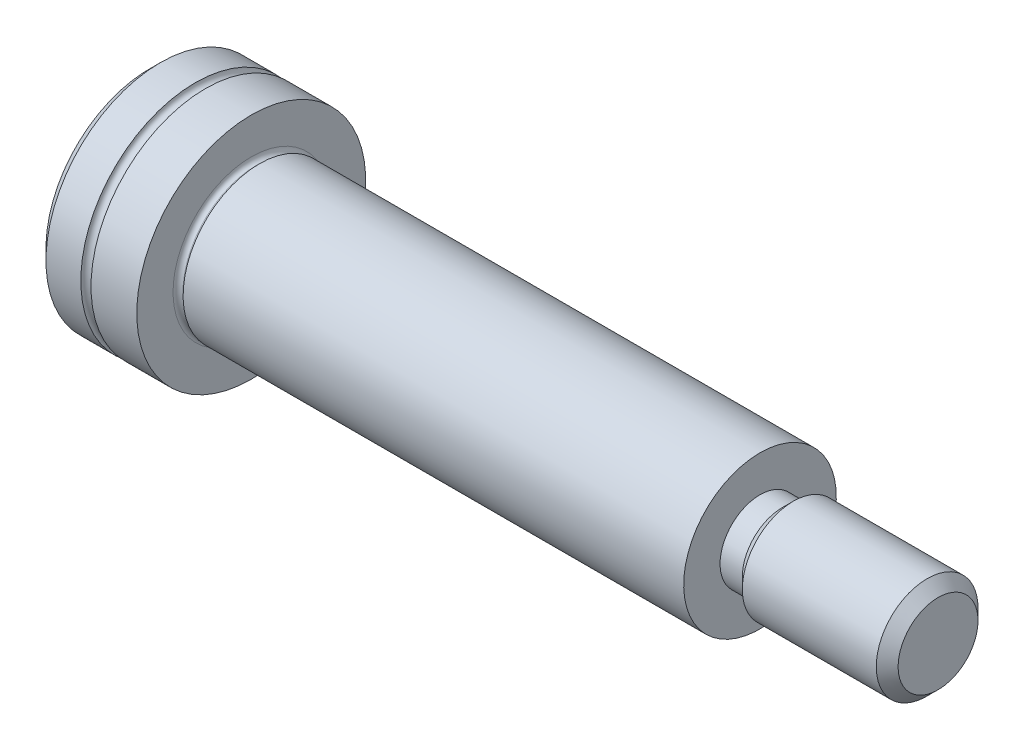
SolidWorks part; units mm, degrees
ref_plane "Front Plane" through (0, 0, 0) normal (0, 0, 1) x (1, 0, 0)
ref_plane "Top Plane" through (0, 0, 0) normal (0, 1, 0) x (1, 0, 0)
ref_plane "Right Plane" through (0, 0, 0) normal (1, 0, 0) x (0, 0, -1)
ref_plane "Plane1" through (0, 0, 0) normal (0, 0, -1) x (-1, 0, 0)
sketch "Sketch1" plane through (0, 0, 0) normal (0, 0, -1) x (-1, 0, 0)
  line L0 (0, 4.5) -> (0, 0)
  line L1 (0, 0) -> (4, 0)
  line L2 (4, 0) -> (4, 4.5)
  line L3 (4, 4.5) -> (2.2, 4.5)
  line L4 (1.8, 4.5) -> (0, 4.5)
  line L5 (0, 0) -> (4, 0) construction
  arc A0 (2.2, 4.5) -> (1.8, 4.5) centre (2, 4.5) cw
revolve "Revolve1" add sketch "Sketch1" angle 360 about L5
sketch "Sketch2" plane through (0, 0, 0) normal (1, 0, 0) x (0, 0, -1)
  circle A0 centre (0, 0) radius 2.88
extrude "Boss-Extrude1" add sketch "Sketch2" along normal blind 0.2507
sketch "Sketch3" plane through (0.2507, 0, 0) normal (1, 0, 0) x (0, 0, -1)
  circle A0 centre (0, 0) radius 2.88
extrude "Boss-Extrude2" add sketch "Sketch3" along normal blind 0.0693 draft 60 draft outward yes
sketch "Sketch4" plane through (0.32, 0, 0) normal (1, 0, 0) x (0, 0, -1)
  circle A0 centre (0, 0) radius 3
extrude "Boss-Extrude3" add sketch "Sketch4" along normal blind 19.68
sketch "Sketch5" plane through (20, 0, 0) normal (1, 0, 0) x (0, 0, -1)
  circle A0 centre (0, 0) radius 1.5705
extrude "Boss-Extrude4" add sketch "Sketch5" along normal blind 0.875
sketch "Sketch6" plane through (20.875, 0, 0) normal (1, 0, 0) x (0, 0, -1)
  circle A0 centre (0, 0) radius 1.5705
extrude "Boss-Extrude5" add sketch "Sketch6" along normal blind 0.4295 draft 45 draft outward yes
sketch "Sketch7" plane through (21.3045, 0, 0) normal (1, 0, 0) x (0, 0, -1)
  circle A0 centre (0, 0) radius 2
extrude "Boss-Extrude6" add sketch "Sketch7" along normal blind 5.6955
sketch "Sketch8" plane through (-4, 0, 0) normal (-1, 0, 0) x (0, 0, 1)
  line L0 (1.5, -0.866) -> (1.5, 0.866)
  line L1 (1.5, 0.866) -> (0, 1.7321)
  line L2 (0, 1.7321) -> (-1.5, 0.866)
  line L3 (-1.5, 0.866) -> (-1.5, -0.866)
  line L4 (-1.5, -0.866) -> (0, -1.7321)
  line L5 (0, -1.7321) -> (1.5, -0.866)
extrude "Cut-Extrude1" cut sketch "Sketch8" against normal blind 2
sketch "Sketch9" plane through (0, 0, 0) normal (0, 0, 1) x (1, 0, 0)
  line L0 (-2, 1.44) -> (-2, 0)
  line L1 (-2, 0) -> (-1.1686, 0)
  line L2 (-1.1686, 0) -> (-2, 1.44)
  line L3 (-2, 0) -> (-1.1686, 0) construction
revolve "Cut-Revolve1" cut sketch "Sketch9" angle 360 about L3
chamfer "Chamfer1" distance 0.4295 angle 45 2 edges at (-4, -4.5, 0) (27, 2, 0)
fillet "Fillet1" radius 0.195 1 edges at (0, 2.88, 0)
